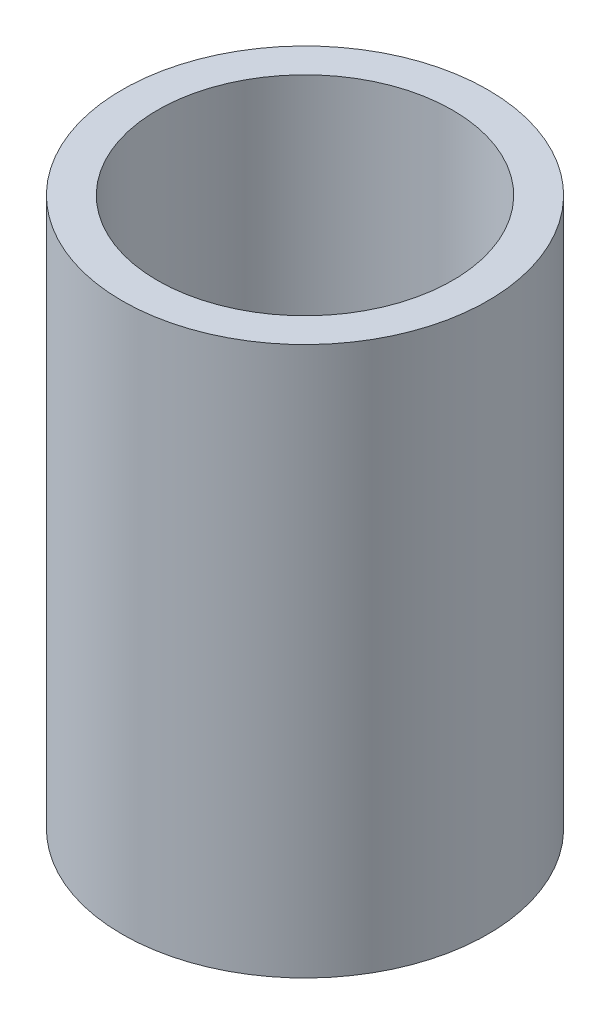
SolidWorks part; units mm, degrees
ref_plane "前视基准面" through (0, 0, 0) normal (0, 0, 1) x (1, 0, 0)
ref_plane "上视基准面" through (0, 0, 0) normal (0, 1, 0) x (1, 0, 0)
ref_plane "右视基准面" through (0, 0, 0) normal (1, 0, 0) x (0, 0, -1)
sketch "草图1" plane through (0, 0, 0) normal (0, 0, 1) x (1, 0, 0)
  line L0 (0, 161.3762) -> (0, 0) construction
  line L1 (141.7365, 0) -> (-131.7984, 0) construction
  line L2 (25.4, 0) -> (25.4, 76.2)
  line L3 (20.5, 76.2) -> (25.4, 76.2)
  line L4 (20.5, 0) -> (25.4, 0)
  line L7 (20.5, 76.2) -> (20.5, 0)
  dimension "D2" = 25.4
  dimension "D3" = 76.2
  dimension "D11" = 20.5
revolve "旋转1" add sketch "草图1" angle 360 about L0
cosmetic thread "装饰螺纹线1" parameters "D2"=42
